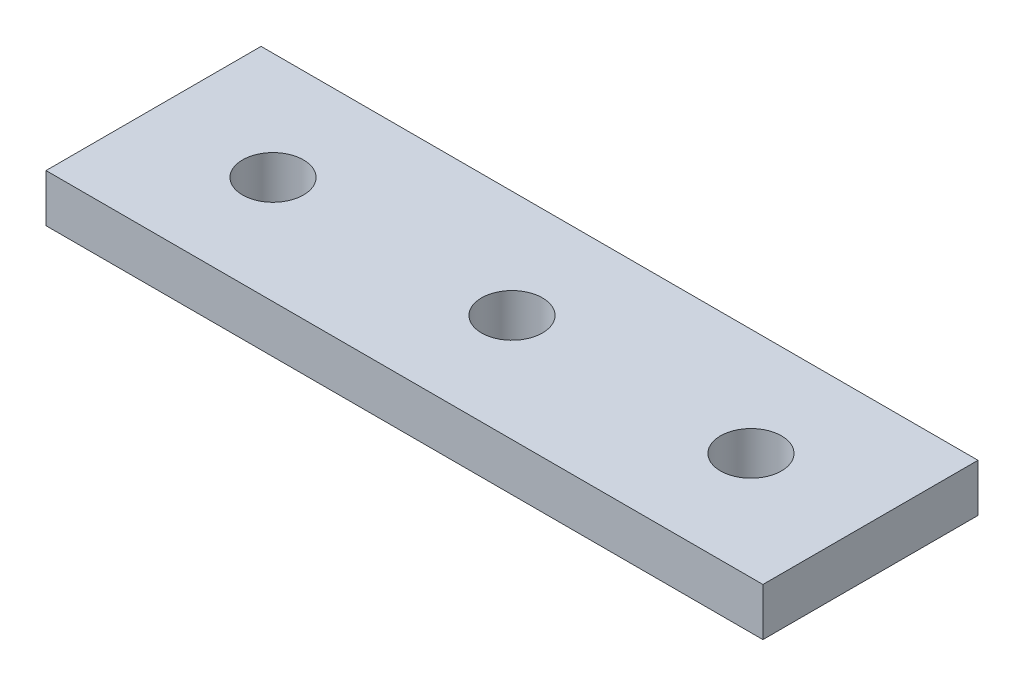
SolidWorks part; units mm, degrees
material "6061-T6 (SS)"
ref_plane "Front Plane" through (0, 0, 0) normal (0, 0, 1) x (1, 0, 0)
ref_plane "Top Plane" through (0, 0, 0) normal (0, 1, 0) x (1, 0, 0)
ref_plane "Right Plane" through (0, 0, 0) normal (1, 0, 0) x (0, 0, -1)
sketch "Sketch1" plane through (0, 0, 0) normal (0, 1, 0) x (1, 0, 0)
  line L0 (0, 0) -> (0, 9) construction
  line L1 (30, -9) -> (-30, -9)
  line L2 (30, -9) -> (30, 9)
  line L3 (30, 9) -> (-30, 9)
  line L4 (-30, -9) -> (-30, 9)
  line L5 (30, -9) -> (-30, 9) construction
  line L6 (30, 9) -> (-30, -9) construction
  circle A0 centre (-20, 0) radius 2.55
  circle A1 centre (20, 0) radius 2.55
  circle A2 centre (0, 0) radius 2.55
  point P0 (0, 0)
  dimension "D3" = 5.1
  dimension "D1" = 18
  dimension "D2" = 60
  dimension "D4" = 40
extrude "Boss-Extrude1" add sketch "Sketch1" along normal blind 4
